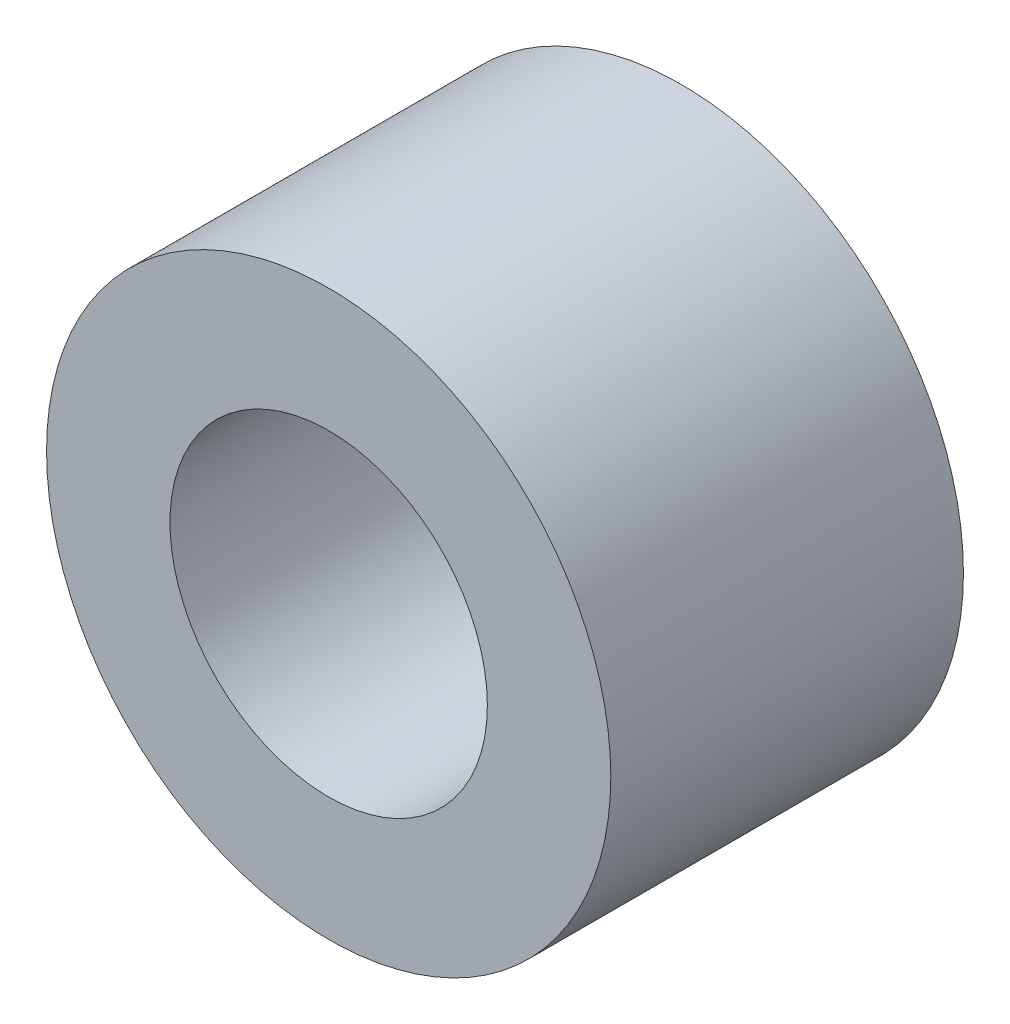
SolidWorks part; units mm, degrees
ref_plane "Plan de face" through (0, 0, 0) normal (0, 0, 1) x (1, 0, 0)
ref_plane "Plan de dessus" through (0, 0, 0) normal (0, 1, 0) x (1, 0, 0)
ref_plane "Plan de droite" through (0, 0, 0) normal (1, 0, 0) x (0, 0, -1)
sketch "Sketch1" plane through (0, 0, 0) normal (0, 0, 1) x (1, 0, 0)
  circle A0 centre (0, 0) radius 4
  circle A1 centre (0, 0) radius 2.25
  dimension "D1" = 4.5
  dimension "D2" = 8
extrude "Boss-Extrude1" add sketch "Sketch1" along normal blind 5
